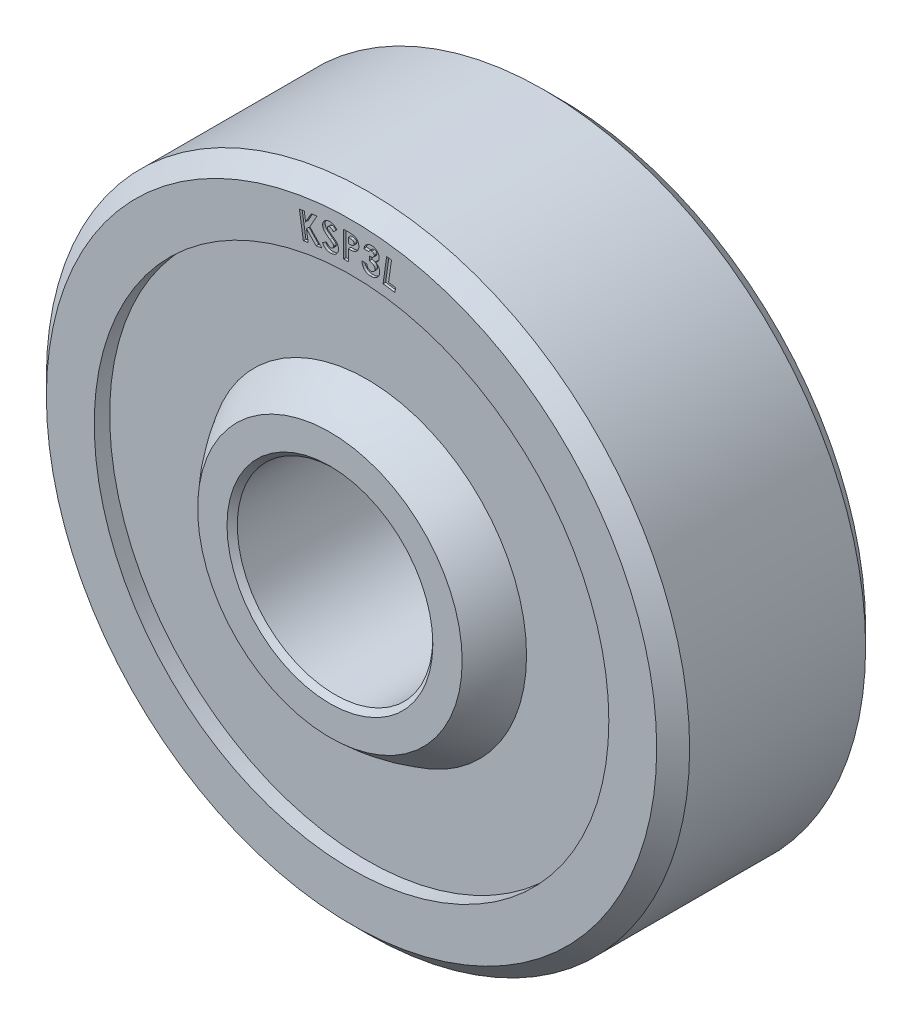
SolidWorks part; units mm, degrees
ref_plane "Front Plane" through (0, 0, 0) normal (0, 0, 1) x (1, 0, 0)
ref_plane "Top Plane" through (0, 0, 0) normal (0, 1, 0) x (1, 0, 0)
ref_plane "Right Plane" through (0, 0, 0) normal (1, 0, 0) x (0, 0, -1)
sketch "Sketch1" plane through (0, 0, 0) normal (1, 0, 0) x (0, 0, -1)
  line L0 (0, 0) -> (63.1482, 0) construction
  line L1 (-3.1115, 2.54) -> (-3.1115, 3.2639)
  line L3 (-2.1971, 3.9379) -> (-2.1971, 6.35)
  line L4 (-2.1971, 6.35) -> (-2.5781, 6.35)
  line L5 (-2.5781, 6.35) -> (-2.5781, 7.5311)
  line L6 (-2.5781, 7.5311) -> (-2.1717, 7.9375)
  line L7 (-2.1717, 7.9375) -> (2.1717, 7.9375)
  line L8 (-2.9845, 2.413) -> (2.9845, 2.413)
  line L9 (0, 0) -> (0, 42.8623) construction
  line L10 (2.5781, 7.5311) -> (2.1717, 7.9375)
  line L11 (2.5781, 6.35) -> (2.5781, 7.5311)
  line L12 (2.1971, 6.35) -> (2.5781, 6.35)
  line L13 (2.1971, 3.9379) -> (2.1971, 6.35)
  line L15 (3.1115, 2.54) -> (3.1115, 3.2639)
  line L16 (-2.9845, 2.413) -> (-3.1115, 2.54)
  line L17 (2.9845, 2.413) -> (3.1115, 2.54)
  arc A0 (3.1115, 3.2639) -> (2.1971, 3.9379) centre (0, 0) ccw
  arc A1 (-2.1971, 3.9379) -> (-3.1115, 3.2639) centre (0, 0) ccw
  point P3 (-3.1115, 2.413)
  point P19 (3.1115, 2.413)
  dimension "D1" = 4.826
  dimension "D2" = 6.5278
  dimension "D3" = 6.223
  dimension "D4" = 5.1562
  dimension "D5" = 0.381
  dimension "D6" = 12.7
  dimension "D7" = 45
  dimension "D8" = 0.4064
  dimension "D9" = 15.875
revolve "Revolve1" add sketch "Sketch1" angle 360 about L0
sketch "Sketch2" plane through (0, 0, 2.5781) normal (0, 0, 1) x (1, 0, 0)
  line L1 (0, 0) -> (0, 5.2337) construction
  arc A0 (-1.2622, 6.4823) -> (1.2622, 6.4823) centre (0, 0) cw construction
  text T0 "KSP3L" font "Century Gothic" height 0.635
  dimension "D1" = 6.604
  dimension "D2" = 2.54
extrude "Cut-Extrude1" cut sketch "Sketch2" against normal blind 0.0635
